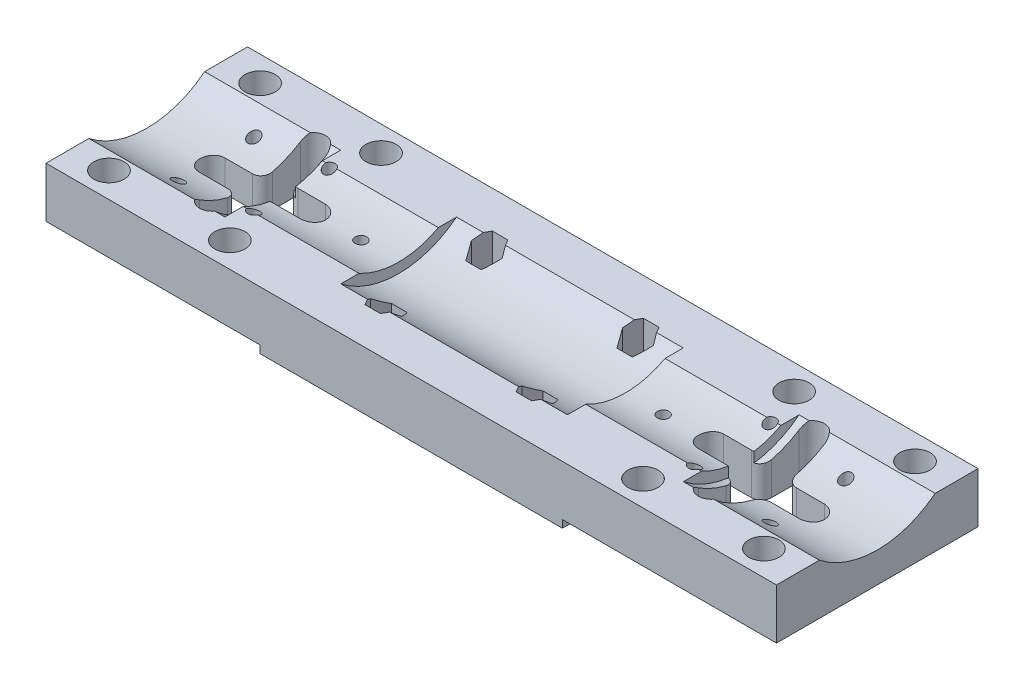
SolidWorks part; units mm, degrees
ref_plane "前视基准面" through (0, 0, 0) normal (0, 0, 1) x (1, 0, 0)
ref_plane "上视基准面" through (0, 0, 0) normal (0, 1, 0) x (1, 0, 0)
ref_plane "右视基准面" through (0, 0, 0) normal (1, 0, 0) x (0, 0, -1)
sketch "草图1" plane through (0, 0, 0) normal (1, 0, 0) x (0, 0, -1)
  line L6 (-20, 10) -> (-20, 0)
  line L7 (-20, 0) -> (20, 0)
  line L8 (20, 10) -> (20, 0)
  line L9 (-20, 24.5) -> (20, 0) construction
  line L10 (-20, 0) -> (20, 24.5) construction
  line L12 (20, 10) -> (11.4891, 10)
  line L13 (0, 0) -> (0, 30.464) construction
  line L14 (-20, 10) -> (-11.4891, 10)
  arc A2 (-11.4891, 10) -> (11.4891, 10) centre (0, 24.5) ccw
  point P0 (0, 12.25)
  point P9 (0, 0)
  point P10 (0, 0)
  point P15 (0, 0)
  point P16 (0, 0)
  dimension "D1" = 18.5
  dimension "D4" = 10
  dimension "D2" = 40
  dimension "D5" = 24.5
extrude "凸台-拉伸1" add sketch "草图1" along normal blind 145
sketch "草图2" plane through (0, 0, 0) normal (0, -1, 0) x (1, 0, 0)
  line L0 (0, 0) -> (177.1338, 0) construction
  line L1 (145, 20) -> (145, -20) construction
  line L2 (137.5, -15) -> (113.5, -15) construction
  line L3 (137.5, -15) -> (137.5, 15) construction
  line L4 (137.5, 15) -> (113.5, 15) construction
  line L5 (113.5, -15) -> (113.5, 15) construction
  line L6 (137.5, -15) -> (113.5, 15) construction
  line L7 (137.5, 15) -> (113.5, -15) construction
  line L8 (72.5, -20) -> (72.5, 20) construction
  line L9 (145, -20) -> (0, -20) construction
  line L10 (145, 20) -> (0, 20) construction
  line L11 (7.5, 15) -> (31.5, -15) construction
  line L12 (7.5, -15) -> (31.5, 15) construction
  line L13 (31.5, -15) -> (31.5, 15) construction
  line L14 (7.5, 15) -> (31.5, 15) construction
  line L15 (7.5, -15) -> (7.5, 15) construction
  line L16 (7.5, -15) -> (31.5, -15) construction
  line L17 (145, 0) -> (-32.1338, 0) construction
  circle A0 centre (137.5, -15) radius 3
  circle A1 centre (113.5, -15) radius 3
  circle A2 centre (113.5, 15) radius 3
  circle A3 centre (137.5, 15) radius 3
  circle A4 centre (7.5, 15) radius 3
  circle A5 centre (31.5, 15) radius 3
  circle A6 centre (31.5, -15) radius 3
  circle A7 centre (7.5, -15) radius 3
  point P3 (125.5, 0)
  point P30 (19.5, 0)
  dimension "D4" = 6
  dimension "D5" = 6
  dimension "D1" = 24
  dimension "D2" = 30
  dimension "D3" = 7.5
extrude "切除-拉伸1" cut sketch "草图2" against normal through all
ref_plane "基准面1" through (27, 0, 0) normal (1, 0, 0) x (0, 0, -1)
sketch "草图3" plane through (27, 0, 0) normal (1, 0, 0) x (0, 0, -1)
  line L2 (11.4891, 10) -> (7.874, 10)
  line L3 (-7.874, 10) -> (-11.4891, 10)
  arc A0 (-11.4891, 10) -> (11.4891, 10) centre (0, 24.5) ccw construction
  arc A1 (-11.4891, 10) -> (11.4891, 10) centre (0, 24.5) ccw
  arc A2 (-7.874, 10) -> (7.874, 10) centre (0, 24.5) ccw
  dimension "D1" = 33
extrude "凸台-拉伸2" add sketch "草图3" along normal blind 23
ref_plane "基准面2" through (72.5, 0, 0) normal (1, 0, 0) x (0, 0, -1)
mirror "镜向1" about plane through (72.5, 0, 0) normal (1, 0, 0) of "凸台-拉伸2"
sketch "草图4" plane through (0, 0, 0) normal (0, -1, 0) x (1, 0, 0)
  line L0 (0, 0) -> (167.0817, 0) construction
  line L1 (72.5, 20) -> (72.5, -20) construction
  line L2 (145, 20) -> (0, 20) construction
  line L3 (145, -20) -> (0, -20) construction
  line L5 (42.5, 20) -> (102.5, 20)
  line L6 (42.5, 20) -> (42.5, -20)
  line L7 (42.5, -20) -> (102.5, -20)
  line L8 (102.5, 20) -> (102.5, -20)
  line L9 (42.5, 20) -> (102.5, -20) construction
  line L10 (42.5, -20) -> (102.5, 20) construction
  point P9 (72.5, 0)
  dimension "D1" = 60
extrude "凸台-拉伸3" add sketch "草图4" along normal blind 1.5
sketch "草图5" plane through (0, -1.5, 0) normal (0, -1, 0) x (1, 0, 0)
  line L0 (0, 0) -> (185.206, 0) construction
  line L1 (72.5, 20) -> (72.5, -44.7016) construction
  line L2 (102.5, 20) -> (42.5, 20) construction
  line L4 (57.5, 10) -> (87.5, 10) construction
  line L5 (57.5, 10) -> (57.5, -10) construction
  line L6 (57.5, -10) -> (87.5, -10) construction
  line L7 (87.5, 10) -> (87.5, -10) construction
  line L8 (57.5, 10) -> (87.5, -10) construction
  line L9 (57.5, -10) -> (87.5, 10) construction
  circle A0 centre (57.5, 10) radius 1.65
  circle A1 centre (87.5, 10) radius 1.65
  circle A2 centre (57.5, 10) radius 1.65
  circle A3 centre (87.5, 10) radius 1.65
  circle A4 centre (57.5, 10) radius 1.65
  circle A5 centre (87.5, 10) radius 1.65
  circle A6 centre (87.5, -10) radius 1.65
  circle A7 centre (57.5, -10) radius 1.65
  point P7 (72.5, 0)
  dimension "D3" = 3.3
  dimension "D1" = 30
  dimension "D2" = 20
extrude "切除-拉伸2" cut sketch "草图5" against normal through all contours A0 | A7 | A6 | A1
sketch "草图6" plane through (0, 10, 0) normal (0, 1, 0) x (1, 0, 0)
  line L1 (60.56, 10) -> (59.03, 12.65)
  line L2 (59.03, 12.65) -> (55.97, 12.65)
  line L3 (55.97, 12.65) -> (54.44, 10)
  line L4 (54.44, 10) -> (55.97, 7.35)
  line L5 (55.97, 7.35) -> (59.03, 7.35)
  line L6 (59.03, 7.35) -> (60.56, 10)
  line L7 (90.56, 10) -> (89.03, 12.65)
  line L8 (89.03, 12.65) -> (85.97, 12.65)
  line L9 (85.97, 12.65) -> (84.44, 10)
  line L10 (84.44, 10) -> (85.97, 7.35)
  line L11 (85.97, 7.35) -> (89.03, 7.35)
  line L12 (89.03, 7.35) -> (90.56, 10)
  line L13 (60.56, -10) -> (59.03, -7.35)
  line L14 (59.03, -7.35) -> (55.97, -7.35)
  line L15 (55.97, -7.35) -> (54.44, -10)
  line L16 (54.44, -10) -> (55.97, -12.65)
  line L17 (55.97, -12.65) -> (59.03, -12.65)
  line L18 (59.03, -12.65) -> (60.56, -10)
  line L19 (90.56, -10) -> (89.03, -7.35)
  line L20 (89.03, -7.35) -> (85.97, -7.35)
  line L21 (85.97, -7.35) -> (84.44, -10)
  line L22 (84.44, -10) -> (85.97, -12.65)
  line L23 (85.97, -12.65) -> (89.03, -12.65)
  line L24 (89.03, -12.65) -> (90.56, -10)
  circle A0 centre (57.5, 10) radius 2.65 construction
  circle A1 centre (87.5, 10) radius 2.65 construction
  circle A2 centre (57.5, -10) radius 2.65 construction
  circle A3 centre (87.5, -10) radius 2.65 construction
  point P27 (0, 0)
  point P39 (0, 0)
  dimension "D1" = 5.3
  dimension "D2" = 5.3
  dimension "D3" = 5.3
  dimension "D4" = 5.3
extrude "切除-拉伸3" cut sketch "草图6" against normal blind 7
sketch "草图7" plane through (0, 0, 0) normal (0, -1, 0) x (1, 0, 0)
  line L0 (0, 0) -> (172.7849, 0) construction
  line L1 (123.75, -20) -> (123.75, 20) construction
  line L2 (145, -20) -> (102.5, -20) construction
  line L3 (145, 20) -> (102.5, 20) construction
  line L4 (72.5, -20) -> (72.5, 20) construction
  line L5 (131.25, -7.5) -> (116.25, -7.5) construction
  line L6 (131.25, -7.5) -> (131.25, 7.5) construction
  line L7 (131.25, 7.5) -> (116.25, 7.5) construction
  line L8 (116.25, -7.5) -> (116.25, 7.5) construction
  line L9 (131.25, -7.5) -> (116.25, 7.5) construction
  line L10 (131.25, 7.5) -> (116.25, -7.5) construction
  line L11 (42.5, -20) -> (102.5, -20) construction
  line L12 (102.5, 20) -> (42.5, 20) construction
  line L13 (13.75, 7.5) -> (28.75, -7.5) construction
  line L14 (13.75, -7.5) -> (28.75, 7.5) construction
  line L15 (28.75, -7.5) -> (28.75, 7.5) construction
  line L16 (13.75, 7.5) -> (28.75, 7.5) construction
  line L17 (13.75, -7.5) -> (13.75, 7.5) construction
  line L18 (13.75, -7.5) -> (28.75, -7.5) construction
  line L19 (21.25, -20) -> (21.25, 20) construction
  line L20 (145, 0) -> (-27.7849, 0) construction
  line L21 (102.5, -20) -> (102.5, 20) construction
  circle A0 centre (131.25, -7.5) radius 1.15
  circle A1 centre (116.25, -7.5) radius 1.15
  circle A2 centre (116.25, 7.5) radius 1.15
  circle A3 centre (131.25, 7.5) radius 1.15
  circle A4 centre (13.75, 7.5) radius 1.15
  circle A5 centre (28.75, 7.5) radius 1.15
  circle A6 centre (28.75, -7.5) radius 1.15
  circle A7 centre (13.75, -7.5) radius 1.15
  circle A8 centre (102.5, 0) radius 1.15
  circle A9 centre (42.5, 0) radius 1.15
  point P9 (123.75, 0)
  point P36 (21.25, 0)
  dimension "D3" = 2.3
  dimension "D4" = 2.3
  dimension "D1" = 15
  dimension "D2" = 15
extrude "切除-拉伸4" cut sketch "草图7" against normal through all
sketch "草图8" plane through (0, 0, 0) normal (0, -1, 0) x (1, 0, 0)
  line L0 (132.0088, 0) -> (112.0088, 0) construction
  line L1 (132.0088, -2.5) -> (124.5088, -2.5)
  line L2 (132.0088, 2.5) -> (124.5088, 2.5)
  line L3 (122.0088, 10) -> (122.0088, -10) construction
  line L4 (124.5088, 10) -> (124.5088, 2.5)
  line L5 (119.5088, 10) -> (119.5088, 2.5)
  line L7 (124.5088, -2.5) -> (124.5088, -10)
  line L8 (119.5088, -2.5) -> (119.5088, -10)
  line L9 (119.5088, -2.5) -> (112.0088, -2.5)
  line L10 (119.5088, 2.5) -> (112.0088, 2.5)
  line L11 (72.5, -20) -> (72.5, 20) construction
  line L12 (42.5, -20) -> (102.5, -20) construction
  line L13 (102.5, 20) -> (42.5, 20) construction
  line L14 (22.9912, 10) -> (22.9912, -10) construction
  line L15 (12.9912, 0) -> (32.9912, 0) construction
  line L16 (25.4912, 2.5) -> (32.9912, 2.5)
  line L17 (25.4912, -2.5) -> (32.9912, -2.5)
  line L18 (25.4912, -2.5) -> (25.4912, -10)
  line L19 (20.4912, -2.5) -> (20.4912, -10)
  line L20 (25.4912, 10) -> (25.4912, 2.5)
  line L21 (20.4912, 10) -> (20.4912, 2.5)
  line L22 (12.9912, 2.5) -> (20.4912, 2.5)
  line L23 (12.9912, -2.5) -> (20.4912, -2.5)
  arc A0 (132.0088, -2.5) -> (132.0088, 2.5) centre (132.0088, 0) ccw
  arc A1 (112.0088, 2.5) -> (112.0088, -2.5) centre (112.0088, 0) ccw
  arc A2 (124.5088, 10) -> (119.5088, 10) centre (122.0088, 10) ccw
  arc A3 (119.5088, -10) -> (124.5088, -10) centre (122.0088, -10) ccw
  arc A4 (25.4912, -10) -> (20.4912, -10) centre (22.9912, -10) cw
  arc A5 (20.4912, 10) -> (25.4912, 10) centre (22.9912, 10) cw
  arc A6 (32.9912, 2.5) -> (32.9912, -2.5) centre (32.9912, 0) cw
  arc A7 (12.9912, -2.5) -> (12.9912, 2.5) centre (12.9912, 0) cw
  point P2 (122.0088, 0)
  point P9 (122.0088, 0)
  point P41 (22.9912, 0)
  dimension "D3" = 2.5
  dimension "D4" = 2.5
  dimension "D1" = 20
  dimension "D2" = 20
extrude "切除-拉伸5" cut sketch "草图8" against normal through all
fillet "圆角1" radius 2 8 edges at (124.5088, 3.0848, -2.5) (119.5088, 3.0848, -2.5) (119.5088, 3.0848, 2.5) (124.5088, 3.0848, 2.5) (20.4912, 3.0848, -2.5) (25.4912, 3.0848, -2.5) (25.4912, 3.0848, 2.5) (20.4912, 3.0848, 2.5)
